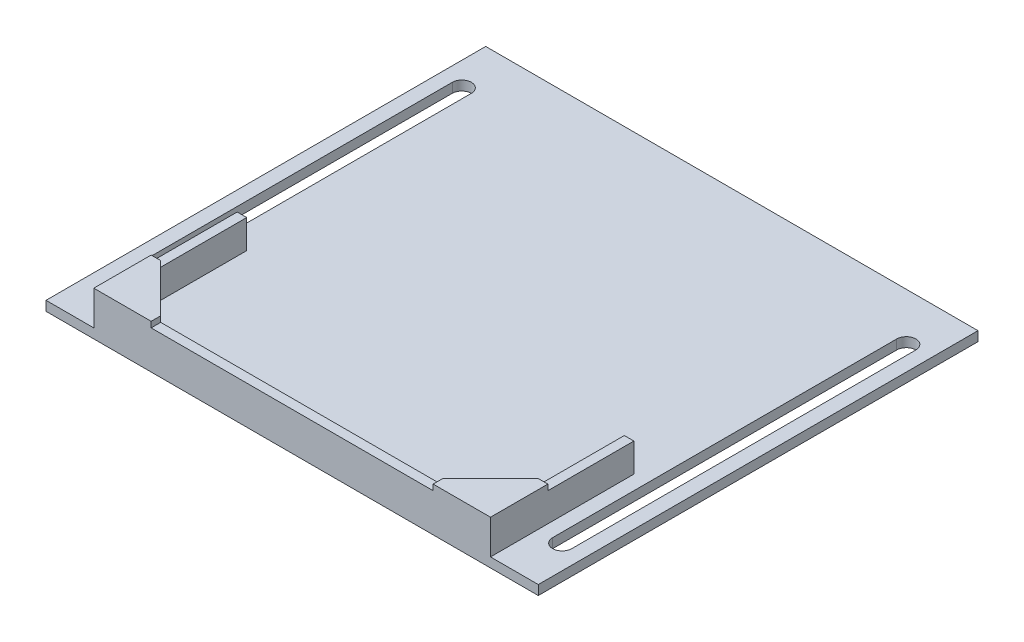
SolidWorks part; units mm, degrees
ref_plane "Alzado" through (0, 0, 0) normal (0, 0, 1) x (1, 0, 0)
ref_plane "Planta" through (0, 0, 0) normal (0, 1, 0) x (1, 0, 0)
ref_plane "Vista lateral" through (0, 0, 0) normal (1, 0, 0) x (0, 0, -1)
sketch "Croquis1" plane through (0, 0, 0) normal (0, 1, 0) x (1, 0, 0)
  line L0 (-2.3216, 1.9) -> (2.3216, 1.9) construction
  line L1 (0, 3) -> (0, -3) construction
  line L2 (3, 0) -> (-3, 0) construction
  line L3 (-2.3216, -1.9) -> (2.3216, -1.9) construction
  line L4 (2.3216, 1.9) -> (-2.3216, 1.9)
  line L5 (2.3216, -1.9) -> (-2.3216, -1.9)
  line L7 (10, -10) -> (-10, -10)
  line L8 (10, -10) -> (10, 10)
  line L9 (10, 10) -> (-10, 10)
  line L10 (-10, -10) -> (-10, 10)
  line L11 (10, -10) -> (-10, 10) construction
  line L12 (10, 10) -> (-10, -10) construction
  circle A0 centre (0, 0) radius 3
  circle A1 centre (0, 0) radius 1.9 construction
  point P11 (0, 1.9)
  dimension "D1" = 6
  dimension "D2" = 3.8
  dimension "D3" = 20
extrude "Saliente-Extruir1" add sketch "Croquis1" along normal blind 5 contours L10 L7 L8 L9 A0 | L5 A0 | L4 A0
sketch "Croquis2" plane through (0, 5, 0) normal (0, 1, 0) x (1, 0, 0)
  line L0 (-39.5, 0) -> (39.5, 0) construction
  line L1 (-10, 10) -> (-39.5, 10)
  line L6 (-39.5, 10) -> (-39.5, 0)
  line L7 (-39.5, 0) -> (-39.5, -80)
  line L8 (-39.5, -80) -> (39.5, -80)
  line L9 (0, 0) -> (0, -80) construction
  line L10 (39.5, 0) -> (39.5, -80)
  line L11 (39.5, 10) -> (39.5, 0)
  line L12 (10, 10) -> (39.5, 10)
  line L13 (-10, 10) -> (10, 10)
  point P0 (0, 0)
  point P4 (0, 0)
  dimension "D1" = 79
  dimension "D2" = 80
extrude "Saliente-Extruir2" add sketch "Croquis2" along normal blind 2
sketch "Croquis3" plane through (0, 5, 0) normal (0, -1, 0) x (1, 0, 0)
  line L0 (39.5, 80) -> (39.5, -10) construction
  line L1 (-39.5, 80) -> (39.5, 80) construction
  line L2 (-39.5, -10) -> (-39.5, 80) construction
  line L3 (39.5, 80) -> (39.5, -10)
  line L4 (-39.5, 80) -> (39.5, 80)
  line L5 (-39.5, -10) -> (-39.5, 80)
  line L11 (-41.5, -10) -> (-41.5, 82)
  line L12 (-41.5, 82) -> (41.5, 82)
  line L13 (41.5, 82) -> (41.5, -10)
  line L14 (-41.5, -10) -> (-39.5, -10)
  line L15 (41.5, -10) -> (39.5, -10)
  dimension "D1" = 2
extrude "Saliente-Extruir3" add sketch "Croquis3" against normal blind 8
sketch "Croquis4" plane through (0, 13, 0) normal (0, 1, 0) x (1, 0, 0)
  line L0 (-29.5, -80) -> (-39.5, -70)
  line L1 (39.5, -70) -> (29.5, -80)
  line L2 (-39.5, -70) -> (-39.5, -80)
  line L3 (-39.5, -80) -> (-29.5, -80)
  line L4 (39.5, -70) -> (39.5, -80)
  line L5 (39.5, -80) -> (29.5, -80)
  line L6 (-39.5, -70) -> (-41.5, -70)
  line L7 (-41.5, -82) -> (-41.5, 10) construction
  line L8 (39.5, -80) -> (-39.5, -80)
  line L9 (-39.5, -80) -> (-39.5, 10)
  line L10 (-39.5, 10) -> (-41.5, 10)
  line L11 (-41.5, 10) -> (-41.5, -82)
  line L12 (-41.5, -82) -> (41.5, -82)
  line L13 (41.5, -82) -> (41.5, 10)
  line L14 (41.5, 10) -> (39.5, 10)
  line L15 (39.5, 10) -> (39.5, -80)
  line L16 (29.5, -80) -> (-29.5, -80)
  line L24 (-29.5, -80) -> (-29.5, -82)
  line L25 (41.5, -82) -> (-41.5, -82) construction
  line L26 (39.5, -70) -> (41.5, -70)
  line L27 (41.5, 10) -> (41.5, -82) construction
  line L28 (29.5, -80) -> (29.5, -82)
  line M9 (39.5, -80) -> (-39.5, -80)
  line M10 (-39.5, -80) -> (-39.5, 10)
  line M12 (-41.5, 10) -> (-41.5, -82)
  line M13 (-41.5, -82) -> (41.5, -82)
  line M14 (41.5, -82) -> (41.5, 10)
  line M16 (39.5, 10) -> (39.5, -80)
  dimension "D1" = 0
extrude "Saliente-Extruir4" add sketch "Croquis4" along normal blind 1.2 contours L0 M9 M10 | L24 L6 M9 M10 M12 M13 | L1 M16 M9 | L28 L26 M9 M13 M14 M16
sketch "Croquis5" plane through (0, 5, 0) normal (0, -1, 0) x (1, 0, 0)
  line L0 (-41.5, 82) -> (-41.5, -10) construction
  line L1 (-41.5, 82) -> (-41.5, -10)
  line L2 (-41.5, 82) -> (-51.5, 82)
  line L3 (-51.5, 82) -> (-51.5, -10)
  line L4 (-51.5, -10) -> (-41.5, -10)
  line L5 (-46.5, 82) -> (-46.5, -10) construction
  line L6 (-46.5, 0) -> (-46.5, 72) construction
  line L7 (-48.5, 0) -> (-48.5, 72)
  line L8 (-44.5, 0) -> (-44.5, 72)
  line L9 (0, 82) -> (0, -10) construction
  line L10 (41.5, 82) -> (-41.5, 82) construction
  line L11 (10, -10) -> (-10, -10) construction
  line L12 (46.5, 0) -> (46.5, 72) construction
  line L13 (48.5, 0) -> (48.5, 72)
  line L14 (44.5, 0) -> (44.5, 72)
  line L15 (41.5, 82) -> (51.5, 82)
  line L16 (41.5, 82) -> (41.5, -10)
  line L17 (51.5, 82) -> (51.5, -10)
  line L18 (51.5, -10) -> (41.5, -10)
  arc A0 (-48.5, 0) -> (-44.5, 0) centre (-46.5, 0) ccw
  arc A1 (-44.5, 72) -> (-48.5, 72) centre (-46.5, 72) ccw
  arc A2 (48.5, 0) -> (44.5, 0) centre (46.5, 0) cw
  arc A3 (44.5, 72) -> (48.5, 72) centre (46.5, 72) cw
  point P6 (-46.5, 0)
  point P9 (-46.5, 36)
  point P22 (46.5, 36)
  dimension "D1" = 10
  dimension "D2" = 10
  dimension "D3" = 10
  dimension "D4" = 4
extrude "Saliente-Extruir5" add sketch "Croquis5" against normal blind 2
sketch "Croquis6" plane through (0, 13, 0) normal (0, 1, 0) x (1, 0, 0)
  line L0 (-41.5, -52) -> (41.5, -52)
  line L1 (-41.5, -70) -> (-41.5, 10) construction
  line L3 (29.5, -82) -> (-29.5, -82) construction
  line L4 (-41.5, -52) -> (-41.5, 10)
  line L5 (-41.5, 10) -> (41.5, 10)
  line L6 (41.5, 10) -> (41.5, -52)
  line L7 (41.5, 10) -> (41.5, -70) construction
  point P4 (34.6975, -52)
  point P8 (0, 0)
  dimension "D1" = 30
extrude "Cortar-Extruir1" cut sketch "Croquis6" against normal up to surface (6 mm away) up to face at (0, 7, 35)
